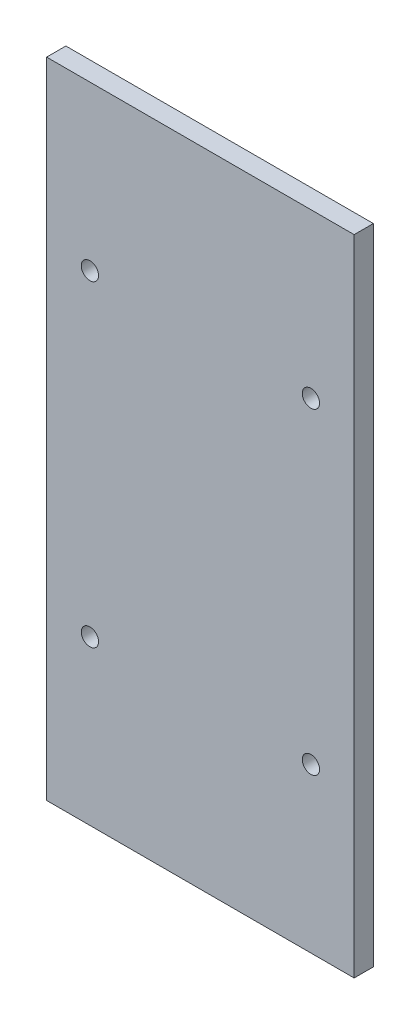
SolidWorks part; units mm, degrees
material "Plain Carbon Steel"
ref_plane "Front Plane" through (0, 0, 0) normal (0, 0, 1) x (1, 0, 0)
ref_plane "Top Plane" through (0, 0, 0) normal (0, 1, 0) x (1, 0, 0)
ref_plane "Right Plane" through (0, 0, 0) normal (1, 0, 0) x (0, 0, -1)
sketch "Sketch1" plane through (0, 0, 0) normal (0, 0, 1) x (1, 0, 0)
  line L0 (150, -600) -> (250, -600) construction
  line L1 (-60, 60) -> (260, 60)
  line L2 (-60, 60) -> (-60, -610)
  line L3 (-60, -610) -> (260, -610)
  line L4 (260, 60) -> (260, -610)
  line L5 (250, 50) -> (250, -600) construction
  line L6 (-50, 50) -> (50, 50) construction
  line L7 (-50, -50) -> (-50, 50) construction
  dimension "D1" = 10
  dimension "D2" = 10
  dimension "D3" = 10
  dimension "D4" = 10
extrude "Boss-Extrude1" add sketch "Sketch1" along normal blind 20 contours L1 L4 L3 L2
sketch "Sketch2" plane through (0, 0, 20) normal (0, 0, 1) x (1, 0, 0)
  circle A0 centre (215, -440) radius 9 construction
  circle A1 centre (-15, -440) radius 9 construction
  circle A2 centre (-15, -110) radius 9 construction
  circle A3 centre (215, -110) radius 9 construction
  circle A4 centre (215, -440) radius 9
  circle A5 centre (-15, -440) radius 9
  circle A6 centre (-15, -110) radius 9
  circle A7 centre (215, -110) radius 9
extrude "Cut-Extrude1" cut sketch "Sketch2" against normal through all
sketch "Sketch3" plane through (0, 0, 0) normal (0, 0, -1) x (-1, 0, 0)
  line L0 (60, 60) -> (60, -610) construction
  line L1 (60, -215) -> (-50, -215)
  line L2 (60, -215) -> (60, -335)
  line L3 (60, -335) -> (-50, -335)
  line L4 (-50, -215) -> (-50, -335)
  line L5 (-260, -275) -> (90, -275) construction
  line L6 (-260, 60) -> (-260, -610) construction
  line L7 (90, -198) -> (90, -352) construction
  dimension "D1" = 120
  dimension "D2" = 110
extrude "Cut-Extrude2" [suppressed] cut sketch "Sketch3" against normal through all
fillet "Fillet1" [suppressed] radius 10
